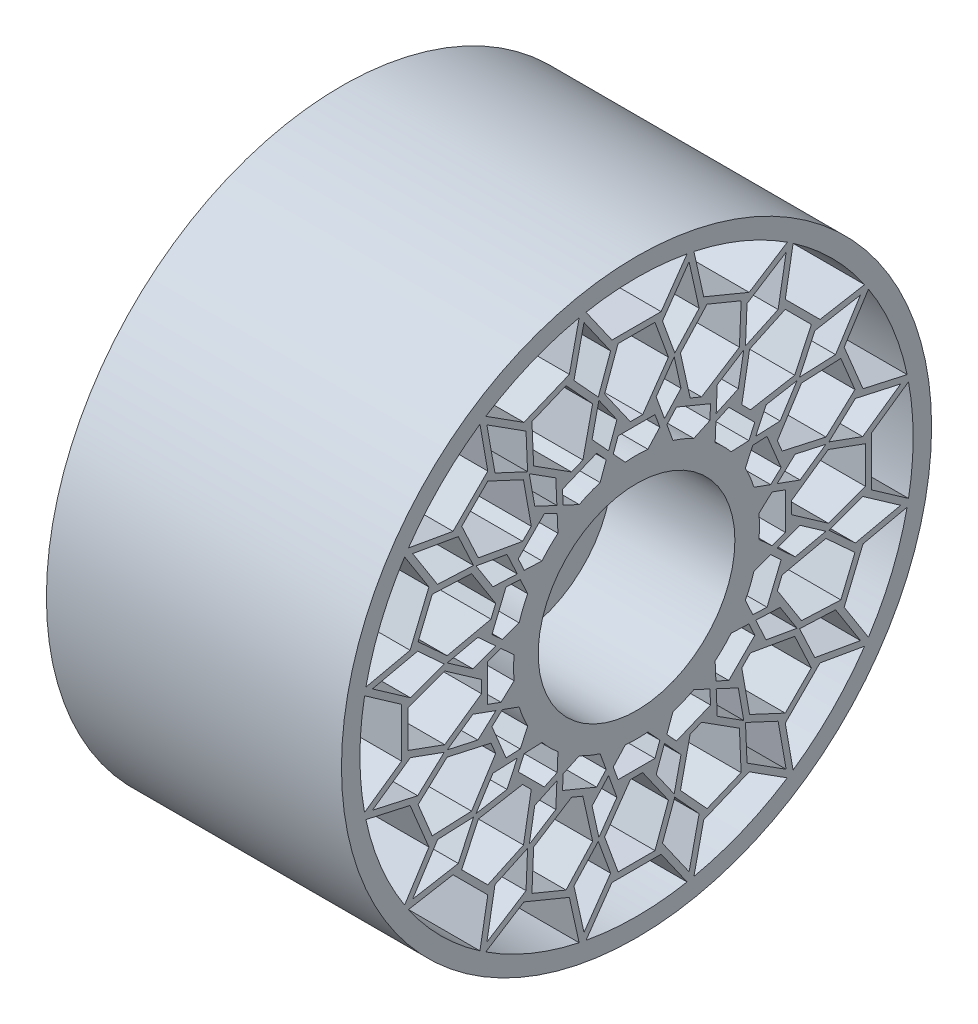
SolidWorks part; units mm, degrees
ref_plane "Front Plane" through (0, 0, 0) normal (0, 0, 1) x (1, 0, 0)
ref_plane "Top Plane" through (0, 0, 0) normal (0, 1, 0) x (1, 0, 0)
ref_plane "Right Plane" through (0, 0, 0) normal (1, 0, 0) x (0, 0, -1)
sketch "Sketch1" plane through (0, 0, 0) normal (1, 0, 0) x (0, 0, -1)
  circle A0 centre (0, 0) radius 152.4
  circle A1 centre (0, 0) radius 50.8
  dimension "D1" = 304.8
  dimension "D2" = 101.6
extrude "Boss-Extrude3" add sketch "Sketch1" along normal blind 63.5
sketch "Sketch2" plane through (63.5, 0, 0) normal (1, 0, 0) x (0, 0, -1)
  line L0 (-26.0977, 140.4713) -> (-12.7, 121.3374)
  line L1 (0, 0) -> (0, 152.4) construction
  line L2 (-12.7, 121.3374) -> (12.7, 121.3374)
  line L3 (12.7, 121.3374) -> (26.0977, 140.4713)
  line L4 (-9.525, 118.1624) -> (9.525, 118.1624)
  line L5 (-9.525, 118.1624) -> (-16.4776, 99.0604)
  line L6 (-16.4776, 99.0604) -> (-3.175, 80.0624)
  line L7 (9.525, 118.1624) -> (16.4776, 99.0604)
  line L8 (16.4776, 99.0604) -> (3.175, 80.0624)
  line L9 (3.175, 80.0624) -> (-3.175, 80.0624)
  line L10 (-9.525, 76.8874) -> (9.525, 76.8874)
  line L11 (-9.525, 76.8874) -> (-15.0567, 61.6891)
  line L12 (9.525, 76.8874) -> (15.0567, 61.6891)
  line L13 (-29.5009, 139.7961) -> (-13.3994, 116.8007)
  line L14 (-13.3994, 116.8007) -> (-20.0264, 98.5932)
  line L15 (-20.0264, 98.5932) -> (-10.1416, 84.4763)
  line L16 (-10.1416, 84.4763) -> (-18.8141, 60.6488)
  line L17 (29.5009, 139.7961) -> (13.3994, 116.8007)
  line L18 (13.3994, 116.8007) -> (20.0264, 98.5932)
  line L19 (20.0264, 98.5932) -> (10.1416, 84.4763)
  line L20 (10.1416, 84.4763) -> (18.8141, 60.6488)
  line L21 (26.2424, 140.4443) -> (32.3183, 113.0375)
  line L22 (29.6449, 139.7657) -> (34.7005, 116.9612)
  line L23 (34.7005, 116.9612) -> (58.1671, 107.2411)
  line L24 (58.1671, 107.2411) -> (77.8671, 119.7914)
  line L25 (80.753, 117.8653) -> (57.0771, 102.7821)
  line L26 (57.0771, 102.7821) -> (56.2319, 83.4245)
  line L27 (54.0187, 105.5228) -> (53.1321, 85.2142)
  line L28 (36.4188, 112.8129) -> (54.0187, 105.5228)
  line L29 (36.4188, 112.8129) -> (22.6855, 97.8256)
  line L30 (32.3183, 113.0375) -> (19.228, 98.752)
  line L31 (19.228, 98.752) -> (22.958, 81.927)
  line L32 (22.6855, 97.8256) -> (27.7052, 75.183)
  line L33 (33.5719, 72.753) -> (27.7052, 75.183)
  line L34 (53.1321, 85.2142) -> (33.5719, 72.753)
  line L35 (56.2319, 83.4245) -> (41.6973, 74.1649)
  line L36 (41.6973, 74.1649) -> (40.5913, 48.8323)
  line L37 (20.6236, 74.6797) -> (38.2235, 67.3896)
  line L38 (38.2235, 67.3896) -> (37.518, 51.2313)
  line L39 (20.6236, 74.6797) -> (9.6968, 62.7553)
  line L40 (22.958, 81.927) -> (5.8273, 63.2321)
  line L41 (77.9905, 119.7111) -> (73.1158, 92.0654)
  line L42 (80.8743, 117.782) -> (76.8182, 94.7787)
  line L43 (76.8182, 94.7787) -> (94.7787, 76.8182)
  line L44 (94.7787, 76.8182) -> (117.782, 80.8743)
  line L45 (119.7111, 77.9905) -> (92.0654, 73.1158)
  line L46 (92.0654, 73.1158) -> (83.8767, 55.5551)
  line L47 (90.2886, 76.8182) -> (81.6977, 58.3949)
  line L48 (76.8182, 90.2886) -> (90.2886, 76.8182)
  line L49 (76.8182, 90.2886) -> (58.3949, 81.6977)
  line L50 (73.1158, 92.0654) -> (55.5551, 83.8767)
  line L51 (55.5551, 83.8767) -> (52.5626, 66.905)
  line L52 (58.3949, 81.6977) -> (54.3676, 58.8577)
  line L53 (58.8577, 54.3676) -> (54.3676, 58.8577)
  line L54 (81.6977, 58.3949) -> (58.8577, 54.3676)
  line L55 (83.8767, 55.5551) -> (66.905, 52.5626)
  line L56 (66.905, 52.5626) -> (56.1888, 29.5816)
  line L57 (47.6324, 61.1028) -> (61.1028, 47.6324)
  line L58 (61.1028, 47.6324) -> (54.2675, 32.9741)
  line L59 (47.6324, 61.1028) -> (32.9741, 54.2675)
  line L60 (52.5626, 66.905) -> (29.5816, 56.1888)
  line L61 (117.8653, 80.753) -> (102.7821, 57.0771)
  line L62 (119.7914, 77.8671) -> (107.2411, 58.1671)
  line L63 (107.2411, 58.1671) -> (116.9612, 34.7005)
  line L64 (116.9612, 34.7005) -> (139.7657, 29.6449)
  line L65 (140.4443, 26.2424) -> (113.0375, 32.3183)
  line L66 (113.0375, 32.3183) -> (98.752, 19.228)
  line L67 (112.8129, 36.4188) -> (97.8256, 22.6855)
  line L68 (105.5228, 54.0187) -> (112.8129, 36.4188)
  line L69 (105.5228, 54.0187) -> (85.2142, 53.1321)
  line L70 (102.7821, 57.0771) -> (83.4245, 56.2319)
  line L71 (83.4245, 56.2319) -> (74.1649, 41.6973)
  line L72 (85.2142, 53.1321) -> (72.753, 33.5719)
  line L73 (75.183, 27.7052) -> (72.753, 33.5719)
  line L74 (97.8256, 22.6855) -> (75.183, 27.7052)
  line L75 (98.752, 19.228) -> (81.927, 22.958)
  line L76 (81.927, 22.958) -> (63.2321, 5.8273)
  line L77 (67.3896, 38.2235) -> (74.6797, 20.6236)
  line L78 (74.6797, 20.6236) -> (62.7553, 9.6968)
  line L79 (67.3896, 38.2235) -> (51.2313, 37.518)
  line L80 (74.1649, 41.6973) -> (48.8323, 40.5913)
  line L81 (139.7961, 29.5009) -> (116.8007, 13.3994)
  line L82 (140.4713, 26.0977) -> (121.3374, 12.7)
  line L83 (121.3374, 12.7) -> (121.3374, -12.7)
  line L84 (121.3374, -12.7) -> (140.4713, -26.0977)
  line L85 (139.7961, -29.5009) -> (116.8007, -13.3994)
  line L86 (116.8007, -13.3994) -> (98.5932, -20.0264)
  line L87 (118.1624, -9.525) -> (99.0604, -16.4776)
  line L88 (118.1624, 9.525) -> (118.1624, -9.525)
  line L89 (118.1624, 9.525) -> (99.0604, 16.4776)
  line L90 (116.8007, 13.3994) -> (98.5932, 20.0264)
  line L91 (98.5932, 20.0264) -> (84.4763, 10.1416)
  line L92 (99.0604, 16.4776) -> (80.0624, 3.175)
  line L93 (80.0624, -3.175) -> (80.0624, 3.175)
  line L94 (99.0604, -16.4776) -> (80.0624, -3.175)
  line L95 (98.5932, -20.0264) -> (84.4763, -10.1416)
  line L96 (84.4763, -10.1416) -> (60.6488, -18.8141)
  line L97 (76.8874, 9.525) -> (76.8874, -9.525)
  line L98 (76.8874, -9.525) -> (61.6891, -15.0567)
  line L99 (76.8874, 9.525) -> (61.6891, 15.0567)
  line L100 (84.4763, 10.1416) -> (60.6488, 18.8141)
  line L101 (140.4443, -26.2424) -> (113.0375, -32.3183)
  line L102 (139.7657, -29.6449) -> (116.9612, -34.7005)
  line L103 (116.9612, -34.7005) -> (107.2411, -58.1671)
  line L104 (107.2411, -58.1671) -> (119.7914, -77.8671)
  line L105 (117.8653, -80.753) -> (102.7821, -57.0771)
  line L106 (102.7821, -57.0771) -> (83.4245, -56.2319)
  line L107 (105.5228, -54.0187) -> (85.2142, -53.1321)
  line L108 (112.8129, -36.4188) -> (105.5228, -54.0187)
  line L109 (112.8129, -36.4188) -> (97.8256, -22.6855)
  line L110 (113.0375, -32.3183) -> (98.752, -19.228)
  line L111 (98.752, -19.228) -> (81.927, -22.958)
  line L112 (97.8256, -22.6855) -> (75.183, -27.7052)
  line L113 (72.753, -33.5719) -> (75.183, -27.7052)
  line L114 (85.2142, -53.1321) -> (72.753, -33.5719)
  line L115 (83.4245, -56.2319) -> (74.1649, -41.6973)
  line L116 (74.1649, -41.6973) -> (48.8323, -40.5913)
  line L117 (74.6797, -20.6236) -> (67.3896, -38.2235)
  line L118 (67.3896, -38.2235) -> (51.2313, -37.518)
  line L119 (74.6797, -20.6236) -> (62.7553, -9.6968)
  line L120 (81.927, -22.958) -> (63.2321, -5.8273)
  line L121 (119.7111, -77.9905) -> (92.0654, -73.1158)
  line L122 (117.782, -80.8743) -> (94.7787, -76.8182)
  line L123 (94.7787, -76.8182) -> (76.8182, -94.7787)
  line L124 (76.8182, -94.7787) -> (80.8743, -117.782)
  line L125 (77.9905, -119.7111) -> (73.1158, -92.0654)
  line L126 (73.1158, -92.0654) -> (55.5551, -83.8767)
  line L127 (76.8182, -90.2886) -> (58.3949, -81.6977)
  line L128 (90.2886, -76.8182) -> (76.8182, -90.2886)
  line L129 (90.2886, -76.8182) -> (81.6977, -58.3949)
  line L130 (92.0654, -73.1158) -> (83.8767, -55.5551)
  line L131 (83.8767, -55.5551) -> (66.905, -52.5626)
  line L132 (81.6977, -58.3949) -> (58.8577, -54.3676)
  line L133 (54.3676, -58.8577) -> (58.8577, -54.3676)
  line L134 (58.3949, -81.6977) -> (54.3676, -58.8577)
  line L135 (55.5551, -83.8767) -> (52.5626, -66.905)
  line L136 (52.5626, -66.905) -> (29.5816, -56.1888)
  line L137 (61.1028, -47.6324) -> (47.6324, -61.1028)
  line L138 (47.6324, -61.1028) -> (32.9741, -54.2675)
  line L139 (61.1028, -47.6324) -> (54.2675, -32.9741)
  line L140 (66.905, -52.5626) -> (56.1888, -29.5816)
  line L141 (80.753, -117.8653) -> (57.0771, -102.7821)
  line L142 (77.8671, -119.7914) -> (58.1671, -107.2411)
  line L143 (58.1671, -107.2411) -> (34.7005, -116.9612)
  line L144 (34.7005, -116.9612) -> (29.6449, -139.7657)
  line L145 (26.2424, -140.4443) -> (32.3183, -113.0375)
  line L146 (32.3183, -113.0375) -> (19.228, -98.752)
  line L147 (36.4188, -112.8129) -> (22.6855, -97.8256)
  line L148 (54.0187, -105.5228) -> (36.4188, -112.8129)
  line L149 (54.0187, -105.5228) -> (53.1321, -85.2142)
  line L150 (57.0771, -102.7821) -> (56.2319, -83.4245)
  line L151 (56.2319, -83.4245) -> (41.6973, -74.1649)
  line L152 (53.1321, -85.2142) -> (33.5719, -72.753)
  line L153 (27.7052, -75.183) -> (33.5719, -72.753)
  line L154 (22.6855, -97.8256) -> (27.7052, -75.183)
  line L155 (19.228, -98.752) -> (22.958, -81.927)
  line L156 (22.958, -81.927) -> (5.8273, -63.2321)
  line L157 (38.2235, -67.3896) -> (20.6236, -74.6797)
  line L158 (20.6236, -74.6797) -> (9.6968, -62.7553)
  line L159 (38.2235, -67.3896) -> (37.518, -51.2313)
  line L160 (41.6973, -74.1649) -> (40.5913, -48.8323)
  line L161 (29.5009, -139.7961) -> (13.3994, -116.8007)
  line L162 (26.0977, -140.4713) -> (12.7, -121.3374)
  line L163 (12.7, -121.3374) -> (-12.7, -121.3374)
  line L164 (-12.7, -121.3374) -> (-26.0977, -140.4713)
  line L165 (-29.5009, -139.7961) -> (-13.3994, -116.8007)
  line L166 (-13.3994, -116.8007) -> (-20.0264, -98.5932)
  line L167 (-9.525, -118.1624) -> (-16.4776, -99.0604)
  line L168 (9.525, -118.1624) -> (-9.525, -118.1624)
  line L169 (9.525, -118.1624) -> (16.4776, -99.0604)
  line L170 (13.3994, -116.8007) -> (20.0264, -98.5932)
  line L171 (20.0264, -98.5932) -> (10.1416, -84.4763)
  line L172 (16.4776, -99.0604) -> (3.175, -80.0624)
  line L173 (-3.175, -80.0624) -> (3.175, -80.0624)
  line L174 (-16.4776, -99.0604) -> (-3.175, -80.0624)
  line L175 (-20.0264, -98.5932) -> (-10.1416, -84.4763)
  line L176 (-10.1416, -84.4763) -> (-18.8141, -60.6488)
  line L177 (9.525, -76.8874) -> (-9.525, -76.8874)
  line L178 (-9.525, -76.8874) -> (-15.0567, -61.6891)
  line L179 (9.525, -76.8874) -> (15.0567, -61.6891)
  line L180 (10.1416, -84.4763) -> (18.8141, -60.6488)
  line L181 (-26.2424, -140.4443) -> (-32.3183, -113.0375)
  line L182 (-29.6449, -139.7657) -> (-34.7005, -116.9612)
  line L183 (-34.7005, -116.9612) -> (-58.1671, -107.2411)
  line L184 (-58.1671, -107.2411) -> (-77.8671, -119.7914)
  line L185 (-80.753, -117.8653) -> (-57.0771, -102.7821)
  line L186 (-57.0771, -102.7821) -> (-56.2319, -83.4245)
  line L187 (-54.0187, -105.5228) -> (-53.1321, -85.2142)
  line L188 (-36.4188, -112.8129) -> (-54.0187, -105.5228)
  line L189 (-36.4188, -112.8129) -> (-22.6855, -97.8256)
  line L190 (-32.3183, -113.0375) -> (-19.228, -98.752)
  line L191 (-19.228, -98.752) -> (-22.958, -81.927)
  line L192 (-22.6855, -97.8256) -> (-27.7052, -75.183)
  line L193 (-33.5719, -72.753) -> (-27.7052, -75.183)
  line L194 (-53.1321, -85.2142) -> (-33.5719, -72.753)
  line L195 (-56.2319, -83.4245) -> (-41.6973, -74.1649)
  line L196 (-41.6973, -74.1649) -> (-40.5913, -48.8323)
  line L197 (-20.6236, -74.6797) -> (-38.2235, -67.3896)
  line L198 (-38.2235, -67.3896) -> (-37.518, -51.2313)
  line L199 (-20.6236, -74.6797) -> (-9.6968, -62.7553)
  line L200 (-22.958, -81.927) -> (-5.8273, -63.2321)
  line L201 (-77.9905, -119.7111) -> (-73.1158, -92.0654)
  line L202 (-80.8743, -117.782) -> (-76.8182, -94.7787)
  line L203 (-76.8182, -94.7787) -> (-94.7787, -76.8182)
  line L204 (-94.7787, -76.8182) -> (-117.782, -80.8743)
  line L205 (-119.7111, -77.9905) -> (-92.0654, -73.1158)
  line L206 (-92.0654, -73.1158) -> (-83.8767, -55.5551)
  line L207 (-90.2886, -76.8182) -> (-81.6977, -58.3949)
  line L208 (-76.8182, -90.2886) -> (-90.2886, -76.8182)
  line L209 (-76.8182, -90.2886) -> (-58.3949, -81.6977)
  line L210 (-73.1158, -92.0654) -> (-55.5551, -83.8767)
  line L211 (-55.5551, -83.8767) -> (-52.5626, -66.905)
  line L212 (-58.3949, -81.6977) -> (-54.3676, -58.8577)
  line L213 (-58.8577, -54.3676) -> (-54.3676, -58.8577)
  line L214 (-81.6977, -58.3949) -> (-58.8577, -54.3676)
  line L215 (-83.8767, -55.5551) -> (-66.905, -52.5626)
  line L216 (-66.905, -52.5626) -> (-56.1888, -29.5816)
  line L217 (-47.6324, -61.1028) -> (-61.1028, -47.6324)
  line L218 (-61.1028, -47.6324) -> (-54.2675, -32.9741)
  line L219 (-47.6324, -61.1028) -> (-32.9741, -54.2675)
  line L220 (-52.5626, -66.905) -> (-29.5816, -56.1888)
  line L221 (-117.8653, -80.753) -> (-102.7821, -57.0771)
  line L222 (-119.7914, -77.8671) -> (-107.2411, -58.1671)
  line L223 (-107.2411, -58.1671) -> (-116.9612, -34.7005)
  line L224 (-116.9612, -34.7005) -> (-139.7657, -29.6449)
  line L225 (-140.4443, -26.2424) -> (-113.0375, -32.3183)
  line L226 (-113.0375, -32.3183) -> (-98.752, -19.228)
  line L227 (-112.8129, -36.4188) -> (-97.8256, -22.6855)
  line L228 (-105.5228, -54.0187) -> (-112.8129, -36.4188)
  line L229 (-105.5228, -54.0187) -> (-85.2142, -53.1321)
  line L230 (-102.7821, -57.0771) -> (-83.4245, -56.2319)
  line L231 (-83.4245, -56.2319) -> (-74.1649, -41.6973)
  line L232 (-85.2142, -53.1321) -> (-72.753, -33.5719)
  line L233 (-75.183, -27.7052) -> (-72.753, -33.5719)
  line L234 (-97.8256, -22.6855) -> (-75.183, -27.7052)
  line L235 (-98.752, -19.228) -> (-81.927, -22.958)
  line L236 (-81.927, -22.958) -> (-63.2321, -5.8273)
  line L237 (-67.3896, -38.2235) -> (-74.6797, -20.6236)
  line L238 (-74.6797, -20.6236) -> (-62.7553, -9.6968)
  line L239 (-67.3896, -38.2235) -> (-51.2313, -37.518)
  line L240 (-74.1649, -41.6973) -> (-48.8323, -40.5913)
  line L241 (-139.7961, -29.5009) -> (-116.8007, -13.3994)
  line L242 (-140.4713, -26.0977) -> (-121.3374, -12.7)
  line L243 (-121.3374, -12.7) -> (-121.3374, 12.7)
  line L244 (-121.3374, 12.7) -> (-140.4713, 26.0977)
  line L245 (-139.7961, 29.5009) -> (-116.8007, 13.3994)
  line L246 (-116.8007, 13.3994) -> (-98.5932, 20.0264)
  line L247 (-118.1624, 9.525) -> (-99.0604, 16.4776)
  line L248 (-118.1624, -9.525) -> (-118.1624, 9.525)
  line L249 (-118.1624, -9.525) -> (-99.0604, -16.4776)
  line L250 (-116.8007, -13.3994) -> (-98.5932, -20.0264)
  line L251 (-98.5932, -20.0264) -> (-84.4763, -10.1416)
  line L252 (-99.0604, -16.4776) -> (-80.0624, -3.175)
  line L253 (-80.0624, 3.175) -> (-80.0624, -3.175)
  line L254 (-99.0604, 16.4776) -> (-80.0624, 3.175)
  line L255 (-98.5932, 20.0264) -> (-84.4763, 10.1416)
  line L256 (-84.4763, 10.1416) -> (-60.6488, 18.8141)
  line L257 (-76.8874, -9.525) -> (-76.8874, 9.525)
  line L258 (-76.8874, 9.525) -> (-61.6891, 15.0567)
  line L259 (-76.8874, -9.525) -> (-61.6891, -15.0567)
  line L260 (-84.4763, -10.1416) -> (-60.6488, -18.8141)
  line L261 (-140.4443, 26.2424) -> (-113.0375, 32.3183)
  line L262 (-139.7657, 29.6449) -> (-116.9612, 34.7005)
  line L263 (-116.9612, 34.7005) -> (-107.2411, 58.1671)
  line L264 (-107.2411, 58.1671) -> (-119.7914, 77.8671)
  line L265 (-117.8653, 80.753) -> (-102.7821, 57.0771)
  line L266 (-102.7821, 57.0771) -> (-83.4245, 56.2319)
  line L267 (-105.5228, 54.0187) -> (-85.2142, 53.1321)
  line L268 (-112.8129, 36.4188) -> (-105.5228, 54.0187)
  line L269 (-112.8129, 36.4188) -> (-97.8256, 22.6855)
  line L270 (-113.0375, 32.3183) -> (-98.752, 19.228)
  line L271 (-98.752, 19.228) -> (-81.927, 22.958)
  line L272 (-97.8256, 22.6855) -> (-75.183, 27.7052)
  line L273 (-72.753, 33.5719) -> (-75.183, 27.7052)
  line L274 (-85.2142, 53.1321) -> (-72.753, 33.5719)
  line L275 (-83.4245, 56.2319) -> (-74.1649, 41.6973)
  line L276 (-74.1649, 41.6973) -> (-48.8323, 40.5913)
  line L277 (-74.6797, 20.6236) -> (-67.3896, 38.2235)
  line L278 (-67.3896, 38.2235) -> (-51.2313, 37.518)
  line L279 (-74.6797, 20.6236) -> (-62.7553, 9.6968)
  line L280 (-81.927, 22.958) -> (-63.2321, 5.8273)
  line L281 (-119.7111, 77.9905) -> (-92.0654, 73.1158)
  line L282 (-117.782, 80.8743) -> (-94.7787, 76.8182)
  line L283 (-94.7787, 76.8182) -> (-76.8182, 94.7787)
  line L284 (-76.8182, 94.7787) -> (-80.8743, 117.782)
  line L285 (-77.9905, 119.7111) -> (-73.1158, 92.0654)
  line L286 (-73.1158, 92.0654) -> (-55.5551, 83.8767)
  line L287 (-76.8182, 90.2886) -> (-58.3949, 81.6977)
  line L288 (-90.2886, 76.8182) -> (-76.8182, 90.2886)
  line L289 (-90.2886, 76.8182) -> (-81.6977, 58.3949)
  line L290 (-92.0654, 73.1158) -> (-83.8767, 55.5551)
  line L291 (-83.8767, 55.5551) -> (-66.905, 52.5626)
  line L292 (-81.6977, 58.3949) -> (-58.8577, 54.3676)
  line L293 (-54.3676, 58.8577) -> (-58.8577, 54.3676)
  line L294 (-58.3949, 81.6977) -> (-54.3676, 58.8577)
  line L295 (-55.5551, 83.8767) -> (-52.5626, 66.905)
  line L296 (-52.5626, 66.905) -> (-29.5816, 56.1888)
  line L297 (-61.1028, 47.6324) -> (-47.6324, 61.1028)
  line L298 (-47.6324, 61.1028) -> (-32.9741, 54.2675)
  line L299 (-61.1028, 47.6324) -> (-54.2675, 32.9741)
  line L300 (-66.905, 52.5626) -> (-56.1888, 29.5816)
  line L301 (-80.753, 117.8653) -> (-57.0771, 102.7821)
  line L302 (-77.8671, 119.7914) -> (-58.1671, 107.2411)
  line L303 (-58.1671, 107.2411) -> (-34.7005, 116.9612)
  line L304 (-34.7005, 116.9612) -> (-29.6449, 139.7657)
  line L305 (-26.2424, 140.4443) -> (-32.3183, 113.0375)
  line L306 (-32.3183, 113.0375) -> (-19.228, 98.752)
  line L307 (-36.4188, 112.8129) -> (-22.6855, 97.8256)
  line L308 (-54.0187, 105.5228) -> (-36.4188, 112.8129)
  line L309 (-54.0187, 105.5228) -> (-53.1321, 85.2142)
  line L310 (-57.0771, 102.7821) -> (-56.2319, 83.4245)
  line L311 (-56.2319, 83.4245) -> (-41.6973, 74.1649)
  line L312 (-53.1321, 85.2142) -> (-33.5719, 72.753)
  line L313 (-27.7052, 75.183) -> (-33.5719, 72.753)
  line L314 (-22.6855, 97.8256) -> (-27.7052, 75.183)
  line L315 (-19.228, 98.752) -> (-22.958, 81.927)
  line L316 (-22.958, 81.927) -> (-5.8273, 63.2321)
  line L317 (-38.2235, 67.3896) -> (-20.6236, 74.6797)
  line L318 (-20.6236, 74.6797) -> (-9.6968, 62.7553)
  line L319 (-38.2235, 67.3896) -> (-37.518, 51.2313)
  line L320 (-41.6973, 74.1649) -> (-40.5913, 48.8323)
  circle A0 centre (0, 0) radius 142.875 construction
  circle A1 centre (0, 0) radius 63.5 construction
  circle A2 centre (0, 0) radius 50.8 construction
  circle A3 centre (0, 0) radius 152.4 construction
  arc A4 (-26.0977, 140.4713) -> (26.0977, 140.4713) centre (0, 0) cw
  arc A5 (-15.0567, 61.6891) -> (15.0567, 61.6891) centre (0, 0) cw
  arc A6 (29.6449, 139.7657) -> (77.8671, 119.7914) centre (0, 0) cw
  arc A7 (9.6968, 62.7553) -> (37.518, 51.2313) centre (0, 0) cw
  arc A8 (80.8743, 117.782) -> (117.782, 80.8743) centre (0, 0) cw
  arc A9 (32.9741, 54.2675) -> (54.2675, 32.9741) centre (0, 0) cw
  arc A10 (119.7914, 77.8671) -> (139.7657, 29.6449) centre (0, 0) cw
  arc A11 (51.2313, 37.518) -> (62.7553, 9.6968) centre (0, 0) cw
  arc A12 (140.4713, 26.0977) -> (140.4713, -26.0977) centre (0, 0) cw
  arc A13 (61.6891, 15.0567) -> (61.6891, -15.0567) centre (0, 0) cw
  arc A14 (139.7657, -29.6449) -> (119.7914, -77.8671) centre (0, 0) cw
  arc A15 (62.7553, -9.6968) -> (51.2313, -37.518) centre (0, 0) cw
  arc A16 (117.782, -80.8743) -> (80.8743, -117.782) centre (0, 0) cw
  arc A17 (54.2675, -32.9741) -> (32.9741, -54.2675) centre (0, 0) cw
  arc A18 (77.8671, -119.7914) -> (29.6449, -139.7657) centre (0, 0) cw
  arc A19 (37.518, -51.2313) -> (9.6968, -62.7553) centre (0, 0) cw
  arc A20 (26.0977, -140.4713) -> (-26.0977, -140.4713) centre (0, 0) cw
  arc A21 (15.0567, -61.6891) -> (-15.0567, -61.6891) centre (0, 0) cw
  arc A22 (-29.6449, -139.7657) -> (-77.8671, -119.7914) centre (0, 0) cw
  arc A23 (-9.6968, -62.7553) -> (-37.518, -51.2313) centre (0, 0) cw
  arc A24 (-80.8743, -117.782) -> (-117.782, -80.8743) centre (0, 0) cw
  arc A25 (-32.9741, -54.2675) -> (-54.2675, -32.9741) centre (0, 0) cw
  arc A26 (-119.7914, -77.8671) -> (-139.7657, -29.6449) centre (0, 0) cw
  arc A27 (-51.2313, -37.518) -> (-62.7553, -9.6968) centre (0, 0) cw
  arc A28 (-140.4713, -26.0977) -> (-140.4713, 26.0977) centre (0, 0) cw
  arc A29 (-61.6891, -15.0567) -> (-61.6891, 15.0567) centre (0, 0) cw
  arc A30 (-139.7657, 29.6449) -> (-119.7914, 77.8671) centre (0, 0) cw
  arc A31 (-62.7553, 9.6968) -> (-51.2313, 37.518) centre (0, 0) cw
  arc A32 (-117.782, 80.8743) -> (-80.8743, 117.782) centre (0, 0) cw
  arc A33 (-54.2675, 32.9741) -> (-32.9741, 54.2675) centre (0, 0) cw
  arc A34 (-77.8671, 119.7914) -> (-29.6449, 139.7657) centre (0, 0) cw
  arc A35 (-37.518, 51.2313) -> (-9.6968, 62.7553) centre (0, 0) cw
  point P10 (0, 121.3374)
  point P15 (0, 80.0624)
  point P16 (0, 118.1624)
  point P23 (0, 76.8874)
  point P42 (0, 142.875)
  point P401 (0, 0)
  dimension "D1" = 12.7
  dimension "D2" = 9.525
  dimension "D3" = 3.175
  dimension "D4" = 3.175
  dimension "D5" = 3.175
  dimension "D6" = 3.175
  dimension "D7" = 3.175
  dimension "D8" = 3.175
  dimension "D9" = 3.175
  dimension "D10" = 3.175
  dimension "D11" = 3.175
  dimension "D12" = 3.175
  dimension "D13" = 25.4
  dimension "D14" = 125
  dimension "D15" = 21.5376
  dimension "D16" = 38.1
  dimension "D17" = 110
  dimension "D18" = 19.05
  dimension "D19" = 6.35
  dimension "D20" = 125
  dimension "D21" = 19.05
  dimension "D22" = 125
  dimension "D23" = 16
extrude "Cut-Extrude1" cut sketch "Sketch2" against normal through all contours A4 L0 L2 L3 | L9 L8 L7 L4 L5 L6 | L316 A5 L40 L12 L10 L11 | L20 A7 L60 L38 L37 L39 | L34 L27 L28 L29 L32 L33 | A6 L22 L23 L24 | A8 L42 L43 L44 | L54 L47 L48 L49 L52 L53 | L36 A9 L80 L58 L57 L59 | L74 L67 L68 L69 L72 L73 | A10 L62 L63 L64 | L56 A11 L100 L78 L77 L79 | L94 L87 L88 L89 L92 L93 | A12 L82 L83 L84 | A14 L102 L103 L104 | L114 L107 L108 L109 L112 L113 | L96 A15 L140 L118 L117 L119 | L116 A17 L160 L138 L137 L139 | L134 L127 L128 L129 L132 L133 | L60 L51 L35 L36 | L50 L41 L25 L26 | L30 L21 L17 L18 | L70 L61 L45 L46 | L80 L71 L55 L56 | L90 L81 L65 L66 | L110 L101 L85 L86 | L120 L111 L95 L96 | L100 L91 L75 L76 | L76 A13 L120 L98 L97 L99 | L130 L121 L105 L106 | L140 L131 L115 L116 | A16 L122 L123 L124 | L150 L141 L125 L126 | A18 L142 L143 L144 | L154 L147 L148 L149 L152 L153 | L160 L151 L135 L136 | L136 A19 L180 L158 L157 L159 | L180 L171 L155 L156 | L170 L161 L145 L146 | A20 L162 L163 L164 | L174 L167 L168 L169 L172 L173 | L156 A21 L200 L178 L177 L179 | L194 L187 L188 L189 L192 L193 | A22 L182 L183 L184 | L176 A23 L220 L198 L197 L199 | L220 L211 L195 L196 | L210 L201 L185 L186 | A24 L202 L203 L204 | L214 L207 L208 L209 L212 L213 | L196 A25 L240 L218 L217 L219 | L240 L231 L215 L216 | L230 L221 L205 L206 | A26 L222 L223 L224 | L234 L227 L228 L229 L232 L233 | L216 A27 L260 L238 L237 L239 | L260 L251 L235 L236 | L250 L241 L225 L226 | A28 L242 L243 L244 | L254 L247 L248 L249 L252 L253 | L236 A29 L280 L258 L257 L259 | L280 L271 L255 L256 | L270 L261 L245 L246 | A30 L262 L263 L264 | L274 L267 L268 L269 L272 L273 | L256 A31 L300 L278 L277 L279 | L300 L291 L275 L276 | L290 L281 L265 L266 | A32 L282 L283 L284 | L294 L287 L288 L289 L292 L293 | L276 A33 L320 L298 L297 L299 | L320 L311 L295 L296 | L310 L301 L285 L286 | A34 L302 L303 L304 | L314 L307 L308 L309 L312 L313 | L296 A35 L16 L318 L317 L319 | L315 L316 L16 L15 | L305 L306 L14 L13 | L190 L181 L165 L166 | L200 L191 L175 L176 | L40 L31 L19 L20
sketch "Sketch4" plane through (0, 0, 0) normal (-1, 0, 0) x (0, 0, 1)
  circle A0 centre (0, 0) radius 152.4
  dimension "D1" = 304.8
extrude "Boss-Extrude5" add sketch "Sketch4" along normal blind 88.9
